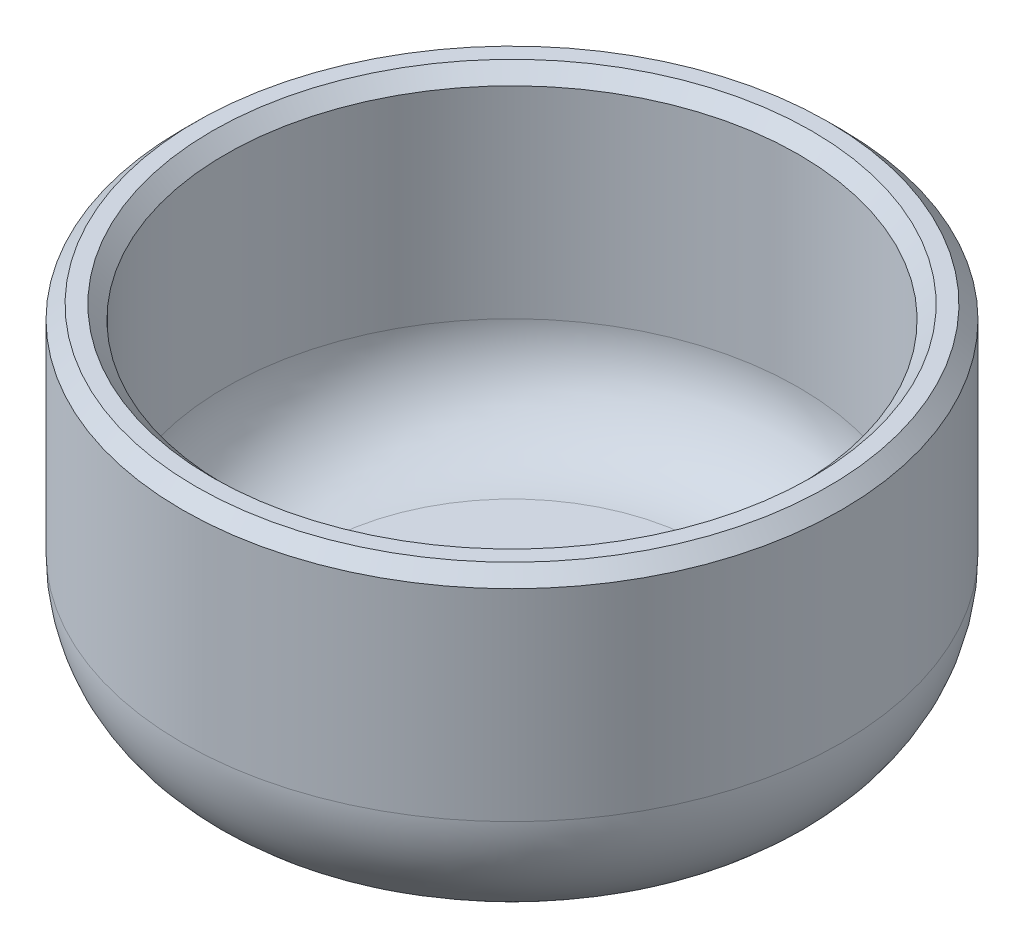
SolidWorks part; units mm, degrees
ref_plane "Ebene vorne" through (0, 0, 0) normal (0, 0, 1) x (1, 0, 0)
ref_plane "Ebene oben" through (0, 0, 0) normal (0, 1, 0) x (1, 0, 0)
ref_plane "Ebene rechts" through (0, 0, 0) normal (1, 0, 0) x (0, 0, -1)
sketch "Skizze1" plane through (0, 0, 0) normal (0, 1, 0) x (1, 0, 0)
  circle A0 centre (0, 0) radius 12.25
  dimension "D1" = 24.5
extrude "Aufsatz-Linear austragen1" add sketch "Skizze1" along normal blind 13
fillet "Verrundung1" radius 5 1 edges at (0, 0, 12.25)
shell "Wandung1" thickness 1.6
chamfer "Fase1" distance 0.5 angle 45 2 edges at (0, 13, 12.25) (0, 13, 10.65)
